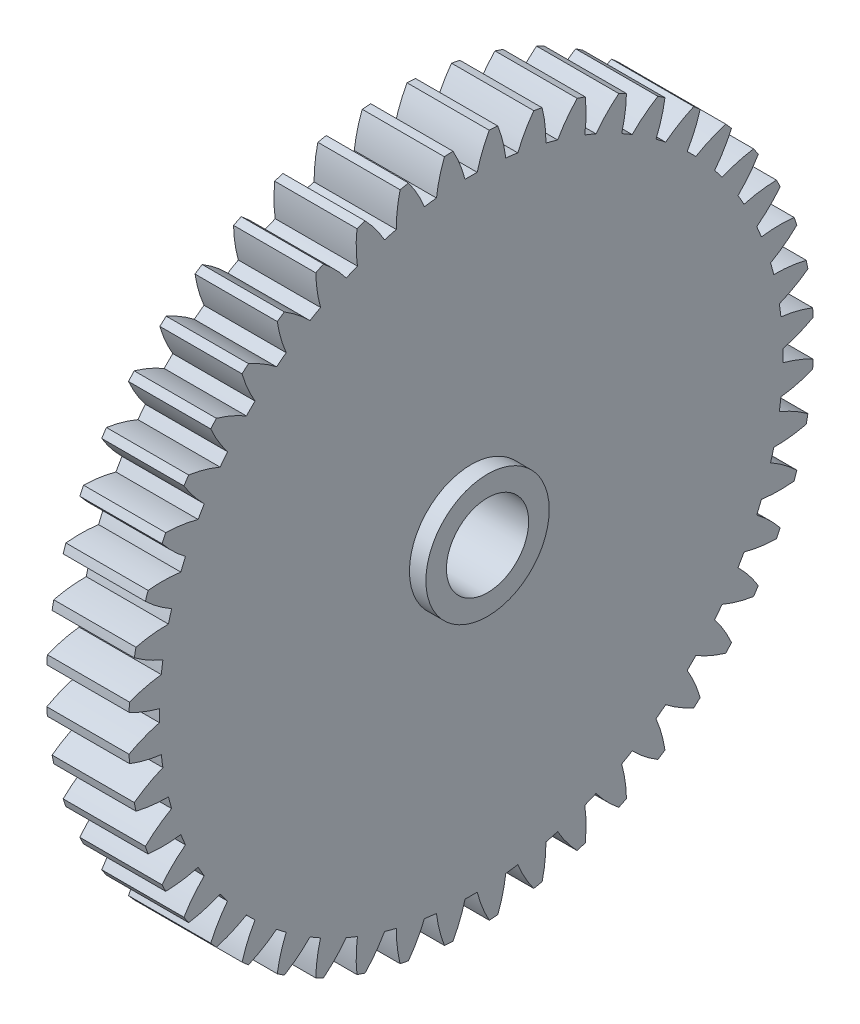
SolidWorks part; units mm, degrees
ref_plane "Plane1" through (0, 0, 0) normal (0, 0, 1) x (1, 0, 0)
ref_plane "Plane2" through (0, 0, 0) normal (0, 1, 0) x (1, 0, 0)
ref_plane "Plane3" through (0, 0, 0) normal (1, 0, 0) x (0, 0, -1)
sketch "HoldingSke" plane through (0, 0, 0) normal (0, 1, 0) x (1, 0, 0)
  line L0 (0, 0) -> (203.951, -226.5105)
  line L1 (-15, 0) -> (100, 0) construction
  line L2 (0, 0) -> (-2.1039, 2.3779)
  line L3 (0, 0) -> (-11.863, 4.5341)
  line L4 (0, 0) -> (5.7786, 6.4178)
  line L5 (0, 0) -> (-47.5972, -17.7524)
  line L6 (0, 0) -> (-10.5278, -7.1032)
  line L7 (-2.1039, 2.3779) -> (8.8308, 51.9871)
  line L8 (-76.2, 54.61) -> (-61.976, 54.61)
  line L9 (-71.009, 38.7566) -> (-53.1078, 45.2721)
  line L10 (-76.2, 71.12) -> (104.1128, 71.12)
  line L11 (0, 0) -> (-12.7, 0)
  line L12 (-76.2, 101.6) -> (-76.1147, 101.6)
  line L13 (24.9733, 27.94) -> (52.9518, 28.4284)
  line L14 (24.9733, 27.94) -> (24.9746, 27.94)
  line L15 (24.9733, 27.94) -> (100.4006, 29.5858)
  circle A0 centre (0, 0) radius 6.35
  circle A1 centre (0, 0) radius 38.1
  circle A2 centre (0, 0) radius 38.1
  circle A3 centre (0, 0) radius 6.35
  dimension "MHD" = 76.2
  dimension "Hub_dia" = 76.2
  dimension "Bore" = 12.7
  dimension "MBD" = 12.7
  dimension "Num_teeth" = 48
  dimension "Pitch" = 304.8
  dimension "Overall_len" = 50.8
  dimension "Show_teeth" = 48
  dimension "Thickness" = 12.7
  dimension "OAL" = 50.8001
  dimension "T_dim" = 14.224
  dimension "Ap" = 20
  dimension "H" = 19.05
  dimension "Pitch_radius" = 180.3128
  dimension "Width" = 12.7
  dimension "Backlash" = 0.0853
  dimension "Addendum_fac" = 1
  dimension "Dedendum_fac" = 1.25
  dimension "Clearance_fac" = 0.25
  dimension "Dedendum_add" = 0.0013
sketch "BasProSke" plane through (0, 0, 0) normal (0, 1, 0) x (1, 0, 0)
  line L0 (-10, 0) -> (60, 0) construction
  line L1 (0, 0) -> (0, 52.9167)
  line L2 (0, 0) -> (12.7, 0)
  line L3 (12.7, 0) -> (12.7, 52.9167)
  line L4 (12.7, 52.9167) -> (0, 52.9167)
  dimension "Thickness" = 12.7
  dimension "Diameter" = 105.8333
revolve "Base-Revolve" add sketch "BasProSke" angle 360 about L0
sketch "TooCutSke" plane through (0, 0, 0) normal (1, 0, 0) x (0, 0, -1)
  line L1 (0, 0) -> (0, 107) construction
  line L2 (0, 0) -> (-1.8115, 50.7677) construction
  line L3 (0, 0) -> (-6.642, 101.3375) construction
  line L4 (-1.8115, 50.7677) -> (-3.321, 50.6688) construction
  arc A0 (0.9387, 48.1437) -> (-0.9387, 48.1437) centre (0, 0) ccw
  arc A1 (2.8166, 52.8671) -> (-2.8166, 52.8671) centre (0, 0) ccw
  circle A2 centre (0, 0) radius 50.8 construction
  circle A3 centre (0, 0) radius 47.7364 construction
  arc A4 (-0.9387, 48.1437) -> (-2.8166, 52.8671) centre (-20.6117, 43.0572) ccw
  arc A5 (2.8166, 52.8671) -> (0.9387, 48.1437) centre (20.6117, 43.0572) ccw
  dimension "Root_dia" = 96.3058
  dimension "Overcut_dia" = 105.8841
  dimension "Pitch_dia" = 101.6
  dimension "Base_dia" = 95.4728
  dimension "Flank_rad" = 20.32
  dimension "Half_ang" = 3.75
  dimension "Half_CT" = 1.5128
extrude "ToothCut" cut sketch "TooCutSke" along normal through all
fillet "Breaks" [suppressed] radius 0.0423
fillet "RootFillets" [suppressed] radius 0.5304
pattern_circular "TeethCuts" count 48 every 7.5 about axis through (-10, 0, 0) along (1, 0, 0) of "ToothCut", "RootFillets", "Breaks"
sketch "HubNeaOneSke" plane through (0, 0, 0) normal (-1, 0, 0) x (0, 0, 1)
  circle A0 centre (0, 0) radius 38.1
  dimension "Diameter" = 76.2
extrude "HubNearOne" [suppressed] add sketch "HubNeaOneSke" along normal blind 38.1001
sketch "HubNeaBotSke" plane through (0, 0, 0) normal (-1, 0, 0) x (0, 0, 1)
  circle A0 centre (0, 0) radius 38.1
  dimension "Diameter" = 76.2
extrude "HubNearBoth" [suppressed] add sketch "HubNeaBotSke" along normal blind 19.05
ref_plane "FarPln" through (12.7, 0, 0) normal (1, 0, 0) x (0, 0, -1)
sketch "HubFarSke" plane through (12.7, 0, 0) normal (1, 0, 0) x (0, 0, -1)
  circle A0 centre (0, 0) radius 38.1
  dimension "Diameter" = 76.2
extrude "HubFar" [suppressed] add sketch "HubFarSke" along normal blind 19.05
sketch "BorSke" plane through (0, 0, 0) normal (1, 0, 0) x (0, 0, -1)
  circle A0 centre (0, 0) radius 6.35
  dimension "Diameter" = 12.7
extrude "Bore" cut sketch "BorSke" along normal mid plane 101.6001
sketch "KeySke" plane through (0, 0, 0) normal (1, 0, 0) x (0, 0, -1)
  line L0 (-1.5875, 0) -> (-1.5875, 7.874)
  line L1 (-1.5875, 7.874) -> (1.5875, 7.874)
  line L2 (1.5875, 7.874) -> (1.5875, 0)
  line L3 (0, 0) -> (0, 34) construction
  line L4 (-1.5875, 0) -> (1.5875, 0)
  dimension "Offset" = 7.874
  dimension "Width" = 3.175
extrude "Keyway" [suppressed] cut sketch "KeySke" along normal mid plane 101.6001
pattern_circular "Keyway2" [suppressed] count 2 every 90 about axis through (-10, 0, 0) along (1, 0, 0)
sketch "Sketch1" plane through (12.7, 0, 0) normal (1, 0, 0) x (0, 0, -1)
  circle A0 centre (0, 0) radius 9.525
  circle A1 centre (0, 0) radius 6.35
  dimension "D1" = 19.05
extrude "Boss-Extrude1" add sketch "Sketch1" along normal blind 2.54
equation "' \"Pitch@HoldingSke\" = 4"
equation "' \"Num_teeth@HoldingSke\" = 12"
equation "' \"Ap@HoldingSke\" =  20"
equation "' \"Ap@HoldingSke\" = 20"
equation "' \"Width@HoldingSke\" = 0.5"
equation "' \"Hub_dia@HoldingSke\"= 1"
equation "' \"Hub_dia@HoldingSke\" = 1"
equation "' \"Overall_len@HoldingSke\" = 1.0"
equation "' \"Bore@HoldingSke\" = 0.75"
equation "' \"T_dim@HoldingSke\" = 0.85"
equation "' \"Width@KeySke\" = 0.25"
equation "' \"Show_teeth@HoldingSke\" = 13"
equation "' \"Backlash@HoldingSke\" = 0.009"
equation "' \"Addendum_fac@HoldingSke\" = 1.0"
equation "' \"Dedendum_fac@HoldingSke\" = 1.25"
equation "' \"Dedendum_add@HoldingSke\" = 0.00005"
equation "' \"Clearance_fac@HoldingSke\" = 0.25"
equation "' \"Pitch@HoldingSke\" = 0.5"
equation "' \"Num_teeth@HoldingSke\" = 23"
equation "' \"Show_teeth@HoldingSke\" = 23"
equation "' \"Backlash@HoldingSke\" = 0.0375"
equation "\"Overcut_dia@TooCutSke\" = (\"Num_teeth@HoldingSke\" + 2 * \"Addendum_fac@HoldingSke\") / \"Pitch@HoldingSke\" + 0.002"
equation "\"Pitch_dia@TooCutSke\" = \"Num_teeth@HoldingSke\" / \"Pitch@HoldingSke\""
equation "\"Base_dia@TooCutSke\" = \"Num_teeth@HoldingSke\" / \"Pitch@HoldingSke\" * cos((\"Ap@HoldingSke\"  * 3.14159265 / 180))"
equation "\"Root_dia@TooCutSke\" = (\"Num_teeth@HoldingSke\" + 2) / \"Pitch@HoldingSke\" - 2 * (\"Addendum_fac@HoldingSke\" + \"Dedendum_fac@HoldingSke\") / \"Pitch@HoldingSke\" - \"Dedendum_add@HoldingSke\" * 2"
equation "\"Half_ang@TooCutSke\" = 180 / \"Num_teeth@HoldingSke\""
equation "\"Half_CT@TooCutSke\" = \"Num_teeth@HoldingSke\" / \"Pitch@HoldingSke\" * sin((3.14159265 / 2 / \"Num_teeth@HoldingSke\")) / 2 - 7 * \"Backlash@HoldingSke\" / 4"
equation "\"Flank_rad@TooCutSke\" = \"Num_teeth@HoldingSke\" / \"Pitch@HoldingSke\" / 5"
equation "\"Radius@RootFillets\" = \"Clearance_fac@HoldingSke\" / \"Pitch@HoldingSke\" + \"Dedendum_add@HoldingSke\""
equation "\"Break_rad@Breaks\" = 0.02 / \"Pitch@HoldingSke\""
equation "\"Thickness@HoldingSke\" = \"Width@HoldingSke\""
equation "\"OAL@HoldingSke\" = \"Thickness@HoldingSke\""
equation "\"MHD@HoldingSke\" = (\"Num_teeth@HoldingSke\" + 2) / \"Pitch@HoldingSke\" - 2 * (\"Addendum_fac@HoldingSke\" + \"Dedendum_fac@HoldingSke\")  / \"Pitch@HoldingSke\" - \"Dedendum_add@HoldingSke\" * 2"
equation "\"MBD@HoldingSke\" = (\"Num_teeth@HoldingSke\" + 2) / \"Pitch@HoldingSke\" - 2 * (\"Addendum_fac@HoldingSke\" + \"Dedendum_fac@HoldingSke\")  / \"Pitch@HoldingSke\" - \"Dedendum_add@HoldingSke\" * 2 - 0.002"
equation "\"MHD@HoldingSke\" = ((sgn( \"MHD@HoldingSke\" - \"Hub_dia@HoldingSke\" )-1)*( \"MHD@HoldingSke\" - \"Hub_dia@HoldingSke\" ))/-2+ \"Hub_dia@HoldingSke\""
equation "\"MBD@HoldingSke\" = ((sgn( \"MBD@HoldingSke\" - \"Bore@HoldingSke\" )-1)*( \"MBD@HoldingSke\" - \"Bore@HoldingSke\" ))/-2+ \"Bore@HoldingSke\""
equation "\"OAL@HoldingSke\" = ((sgn( \"OAL@HoldingSke\" - \"Overall_len@HoldingSke\" )+1)*( \"OAL@HoldingSke\" - \"Overall_len@HoldingSke\" ))/2 + \"Overall_len@HoldingSke\" + 0.000002"
equation "\"Num_teeth@TeethCuts\" = int( \"Show_teeth@HoldingSke\" ) + 1"
equation "\"Num_teeth@TeethCuts\" = ((sgn( \"Num_teeth@TeethCuts\" - \"Num_teeth@HoldingSke\" )-1)*( \"Num_teeth@TeethCuts\" - \"Num_teeth@HoldingSke\" ))/-2+ \"Num_teeth@HoldingSke\""
equation "\"Num_teeth@TeethCuts\" = ((sgn( \"Num_teeth@TeethCuts\" - 2.0)+1)*( \"Num_teeth@TeethCuts\" - 2.0))/2 +2.0"
equation "\"Angle@TeethCuts\" = 360.0 / \"Num_teeth@HoldingSke\""
equation "\"Diameter@BasProSke\" = (\"Num_teeth@HoldingSke\" + 2 * \"Addendum_fac@HoldingSke\") / \"Pitch@HoldingSke\""
equation "\"Thickness@BasProSke\"  = \"Thickness@HoldingSke\""
equation "' \"Fillet_rad@BasProSke\" =  \"Thickness@HoldingSke\" * 0.05"
equation "' \"Fillet_rad@BasProSke\" = \"Thickness@HoldingSke\" * 0.05"
equation "\"MHD@HoldingSke\" = ((sgn( \"MHD@HoldingSke\" - \"Root_dia@TooCutSke\" )-1)*( \"MHD@HoldingSke\" - \"Root_dia@TooCutSke\" ))/-2+ \"Root_dia@TooCutSke\""
equation "\"Diameter@HubNeaOneSke\" = \"MHD@HoldingSke\""
equation "\"Length@HubNearOne\" = \"OAL@HoldingSke\" - \"Thickness@BasProSke\""
equation "\"Diameter@HubNeaBotSke\" = \"MHD@HoldingSke\""
equation "\"Length@HubNearBoth\" = ( \"OAL@HoldingSke\" - \"Thickness@BasProSke\" ) / 2.0"
equation "\"Thickness@FarPln\" = \"Thickness@BasProSke\""
equation "\"Diameter@HubFarSke\" = \"MHD@HoldingSke\""
equation "\"Length@HubFar\" = ( \"OAL@HoldingSke\" - \"Thickness@BasProSke\" ) / 2.0"
equation "\"Diameter@BorSke\" = \"MBD@HoldingSke\""
equation "\"D1@Bore\" = \"OAL@HoldingSke\" * 2.0"
equation "\"D1@Keyway\" = \"OAL@HoldingSke\" * 2.0"
equation "\"Offset@KeySke\" = \"T_dim@HoldingSke\" - \"MBD@HoldingSke\" / 2.0"
